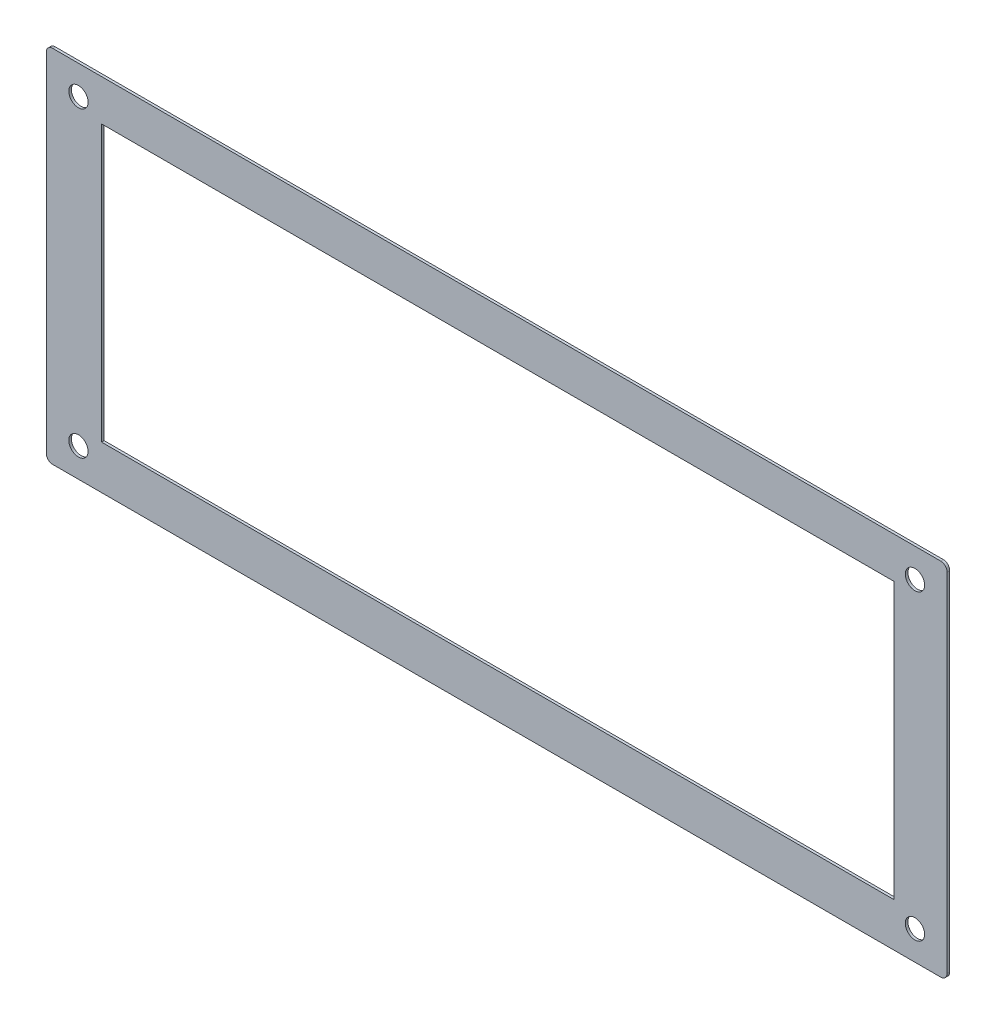
SolidWorks part; units mm, degrees
ref_plane "Front Plane" through (0, 0, 0) normal (0, 0, 1) x (1, 0, 0)
ref_plane "Top Plane" through (0, 0, 0) normal (0, 1, 0) x (1, 0, 0)
ref_plane "Right Plane" through (0, 0, 0) normal (1, 0, 0) x (0, 0, -1)
sketch "Sketch1" plane through (0, 0, 0) normal (0, 0, 1) x (1, 0, 0)
  line L0 (5, 51.5) -> (135, 51.5) construction
  line L1 (1, 0) -> (139, 0)
  line L2 (0, 1) -> (0, 55)
  line L3 (1, 56) -> (139, 56)
  line L4 (140, 1) -> (140, 55)
  line L5 (5, 51.5) -> (5, 4.5) construction
  line L7 (3, 54.5) -> (137, 54.5)
  line L8 (2, 53.5) -> (2, 2.5)
  line L9 (3, 1.5) -> (137, 1.5)
  line L10 (138, 53.5) -> (138, 2.5)
  line L11 (8.6049, 49.6332) -> (131.7338, 49.6332)
  line L12 (8.6049, 49.6332) -> (8.6049, 6.8028)
  line L13 (8.6049, 6.8028) -> (131.7338, 6.8028)
  line L14 (131.7338, 49.6332) -> (131.7338, 6.8028)
  circle A0 centre (5, 51.5) radius 1.5
  circle A1 centre (5, 4.5) radius 1.5
  circle A2 centre (135, 4.5) radius 1.5
  circle A3 centre (135, 51.5) radius 1.5
  arc A4 (139, 56) -> (140, 55) centre (139, 55) cw
  arc A5 (137, 54.5) -> (138, 53.5) centre (137, 53.5) cw
  arc A6 (137, 1.5) -> (138, 2.5) centre (137, 2.5) ccw
  arc A7 (139, 0) -> (140, 1) centre (139, 1) ccw
  arc A8 (2, 2.5) -> (3, 1.5) centre (3, 2.5) ccw
  arc A9 (1, 0) -> (0, 1) centre (1, 1) cw
  arc A10 (0, 55) -> (1, 56) centre (1, 55) cw
  arc A11 (3, 54.5) -> (2, 53.5) centre (3, 53.5) ccw
  point P13 (70, 51.5)
  point P14 (70, 56)
  point P15 (5, 28)
  point P16 (0, 28)
  point P21 (70, 54.5)
  point P22 (138, 28)
  point P27 (138, 54.5)
  point P30 (138, 1.5)
  point P33 (140, 0)
  point P38 (0, 0)
  point P41 (0, 56)
  point P44 (2, 54.5)
  dimension "D1" = 3
  dimension "D5" = 47
  dimension "D8" = 1
  dimension "D2" = 130
  dimension "D3" = 140
  dimension "D4" = 56
  dimension "D6" = 136
  dimension "D7" = 53
extrude "Boss-Extrude1" add sketch "Sketch1" against normal blind 0.4 contours L10 L7 L8 L9 A3 A2 A1 A0 | L1 L4 L3 L2 L7 L10 L9 L8
